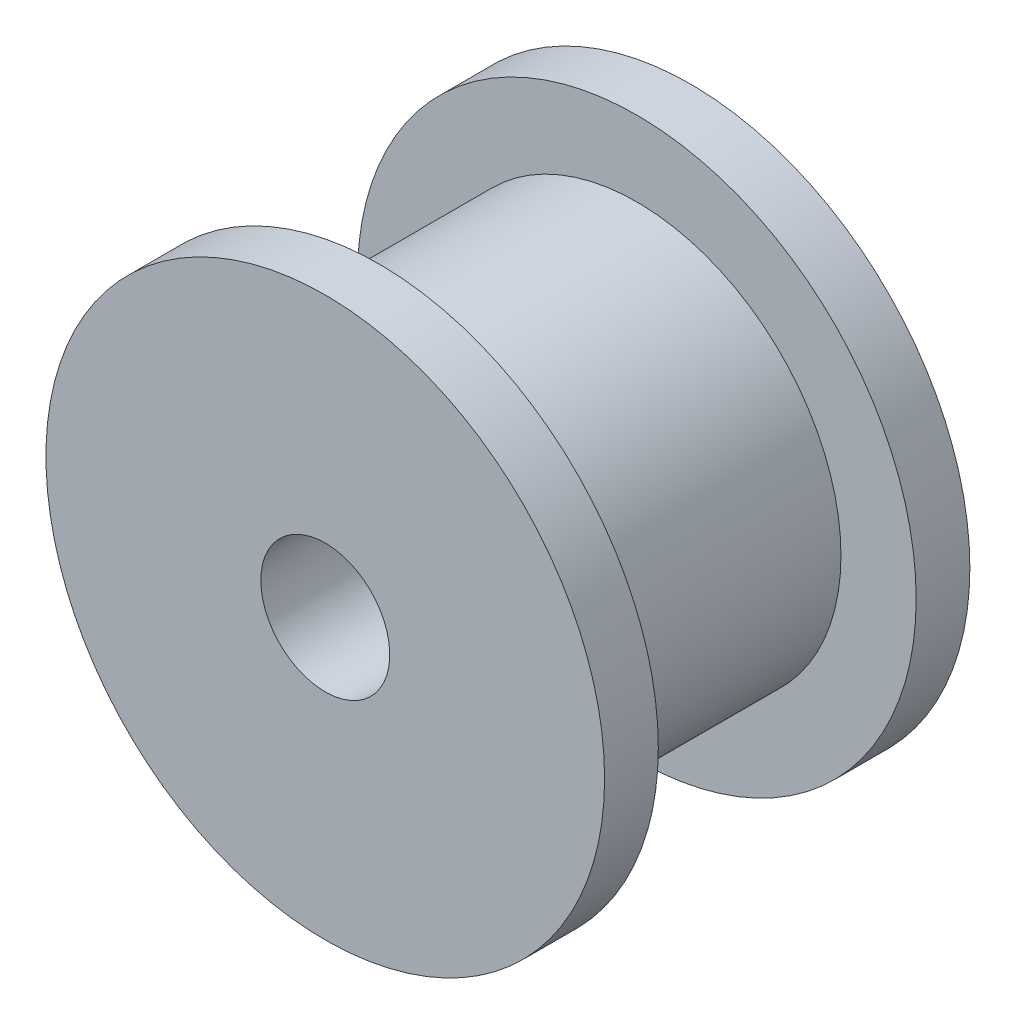
SolidWorks part; units mm, degrees
ref_plane "前视基准面" through (0, 0, 0) normal (0, 0, 1) x (1, 0, 0)
ref_plane "上视基准面" through (0, 0, 0) normal (0, 1, 0) x (1, 0, 0)
ref_plane "右视基准面" through (0, 0, 0) normal (1, 0, 0) x (0, 0, -1)
sketch "草图1" plane through (0, 0, 0) normal (0, 0, 1) x (1, 0, 0)
  circle A0 centre (0, 0) radius 6.5
  dimension "D1" = 13
extrude "凸台-拉伸1" add sketch "草图1" along normal blind 1.25
sketch "草图2" plane through (0, 0, 1.25) normal (0, 0, 1) x (1, 0, 0)
  circle A0 centre (0, 0) radius 4.75
  dimension "D1" = 9.5
extrude "凸台-拉伸2" add sketch "草图2" along normal blind 6
sketch "草图3" plane through (0, 0, 7.25) normal (0, 0, 1) x (1, 0, 0)
  circle A0 centre (0, 0) radius 6.5
  dimension "D1" = 13
extrude "凸台-拉伸3" add sketch "草图3" along normal blind 1.25
sketch "草图4" plane through (0, 0, 0) normal (0, 0, -1) x (-1, 0, 0)
  circle A0 centre (0, 0) radius 1.5
  dimension "D1" = 3
extrude "切除-拉伸1" cut sketch "草图4" against normal through all
